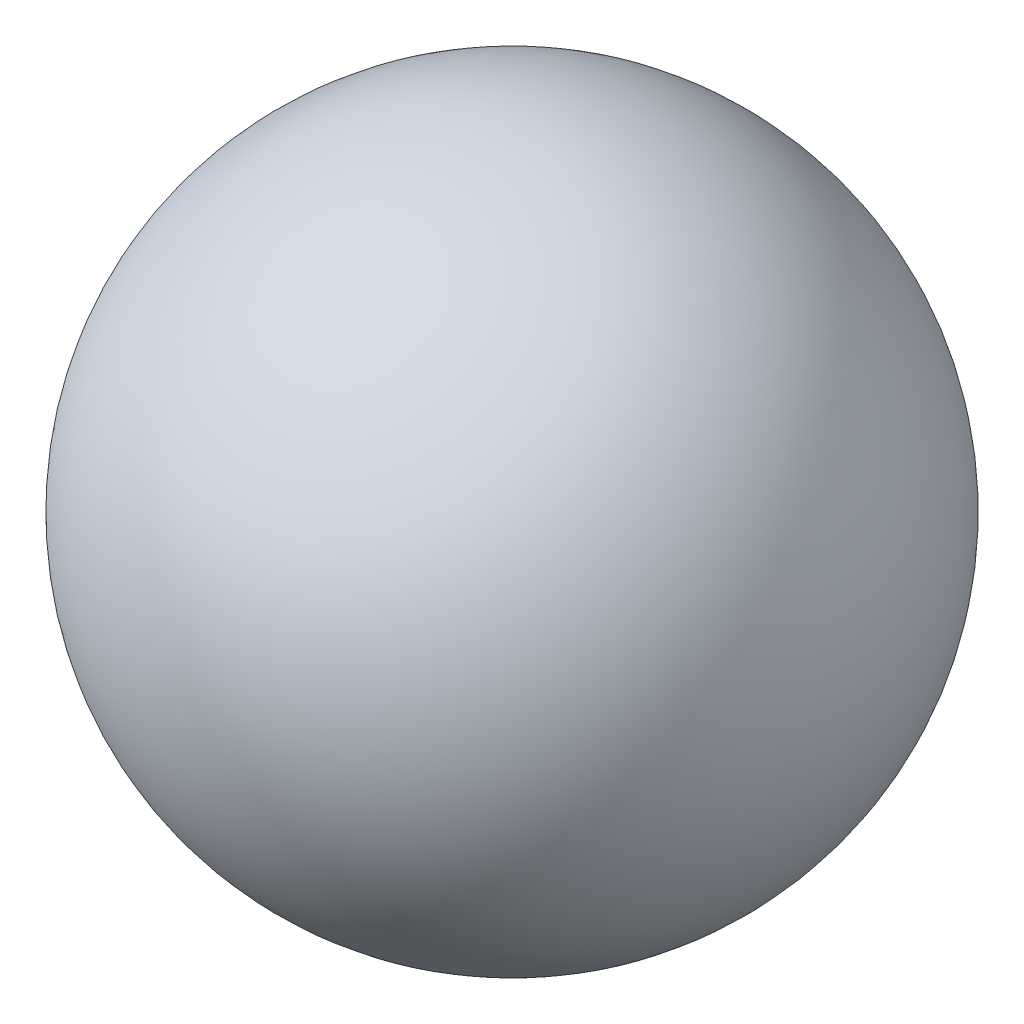
SolidWorks part; units mm, degrees
ref_plane "Front Plane" through (0, 0, 0) normal (0, 0, 1) x (1, 0, 0)
ref_plane "Top Plane" through (0, 0, 0) normal (0, 1, 0) x (1, 0, 0)
ref_plane "Right Plane" through (0, 0, 0) normal (1, 0, 0) x (0, 0, -1)
sketch "Sketch1" plane through (0, 0, 0) normal (0, 0, 1) x (1, 0, 0)
  line L0 (0, 25.4) -> (0, -25.4) construction
  line L1 (0, 25.4) -> (0, -25.4)
  arc A0 (0, -25.4) -> (0, 25.4) centre (0, 0) ccw
revolve "Revolve1" add sketch "Sketch1" angle 360 about L0
